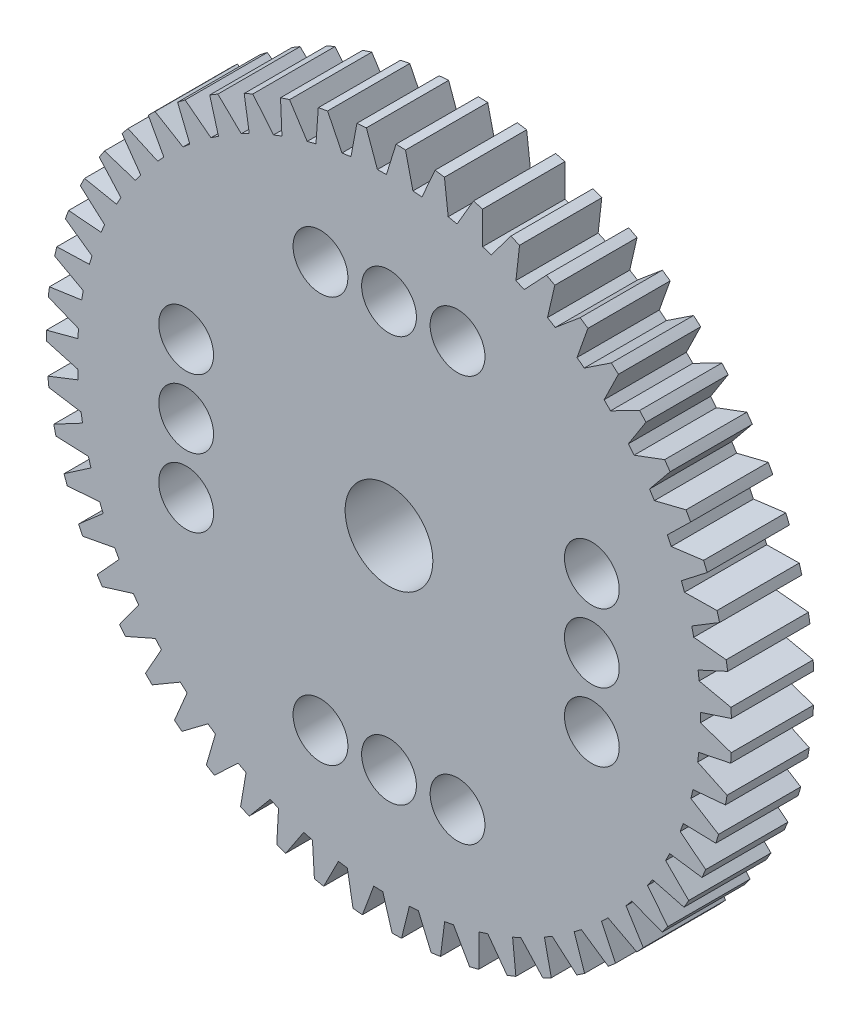
SolidWorks part; units mm, degrees
other "Markup1"
sketch "Sketch3" plane through (-11.5, 11.4999, 3) normal (-0.0441, 0.0247, 0.9987) x (0.9973, -0.0583, 0.0455)
ref_plane "Front Plane" through (0, 0, 0) normal (0, 0, 1) x (1, 0, 0)
ref_plane "Top Plane" through (0, 0, 0) normal (0, 1, 0) x (1, 0, 0)
ref_plane "Right Plane" through (0, 0, 0) normal (1, 0, 0) x (0, 0, -1)
sketch "Sketch1" plane through (0, 0, 0) normal (0, 0, 1) x (1, 0, 0)
  line L2 (-2.5, 7.4) -> (2.5, 7.4) construction
  line L3 (-2.5, -7.4) -> (2.5, -7.4) construction
  line L4 (-7.4, -2.5) -> (-7.4, 2.5) construction
  line L5 (7.4, -2.5) -> (7.4, 2.5) construction
  circle A0 centre (0, 0) radius 12.5
  circle A1 centre (0, 0) radius 10.5 construction
  circle A2 centre (0, 0) radius 1.6
  circle A3 centre (-2.5, 7.4) radius 1
  circle A4 centre (0, 7.4) radius 1
  circle A5 centre (2.5, 7.4) radius 1
  circle A6 centre (2.5, -7.4) radius 1
  circle A7 centre (0, -7.4) radius 1
  circle A8 centre (-2.5, -7.4) radius 1
  circle A9 centre (7.4, -2.5) radius 1
  circle A10 centre (7.4, 0) radius 1
  circle A11 centre (7.4, 2.5) radius 1
  circle A12 centre (-7.4, 2.5) radius 1
  circle A13 centre (-7.4, 0) radius 1
  circle A14 centre (-7.4, -2.5) radius 1
  dimension "D1" = 25
  dimension "D2" = 21
  dimension "3,2" = 3.2
  dimension "D4" = 2
  dimension "D5" = 2
  dimension "D6" = 2
  dimension "D10" = 2
  dimension "D11" = 2
  dimension "D12" = 2
  dimension "D7" = 2.5
  dimension "D8" = 2.5
  dimension "D9" = 7.4
  dimension "D13" = 2.5
  dimension "D14" = 2.5
  dimension "D15" = 7.4
extrude "Boss-Extrude1" add sketch "Sketch1" along normal blind 3
sketch "Sketch2" plane through (0, 0, 3) normal (0, 0, 1) x (1, 0, 0)
  line L0 (-6.5438, 10.6642) -> (-7.4471, 10.0542)
  line L1 (-7.4471, 10.0542) -> (-6.4952, 9.3236)
  line L2 (-6.4952, 9.3236) -> (-6.2217, 9.5083)
  line L3 (-6.2217, 9.5083) -> (-6.5438, 10.6642)
  line L4 (-6.4952, 9.3236) -> (-7.5228, 8.6296) construction
  line L5 (-7.5228, 8.6296) -> (-7.8449, 9.7856) construction
  line L6 (-7.8449, 9.7856) -> (-7.4471, 10.0542) construction
  circle A0 centre (0, 0) radius 11.9362 construction
  circle A1 centre (0, 0) radius 12.5 construction
  point P11 (-6.3827, 10.0863)
  point P12 (-6.9711, 9.6889)
  dimension "D1" = 1.09
  dimension "D2" = 0.33
  dimension "D3" = 1.2
  dimension "D4" = 1.2
  dimension "D5" = 1.24
  dimension "D6" = 0.48
  dimension "D7" = 1.2
extrude "Cut-Extrude1" cut sketch "Sketch2" against normal blind 3
pattern_circular "CirPattern1" count 55 over 360 about axis through (0, 0, 0) along (0, 0, 1) of "Cut-Extrude1"
